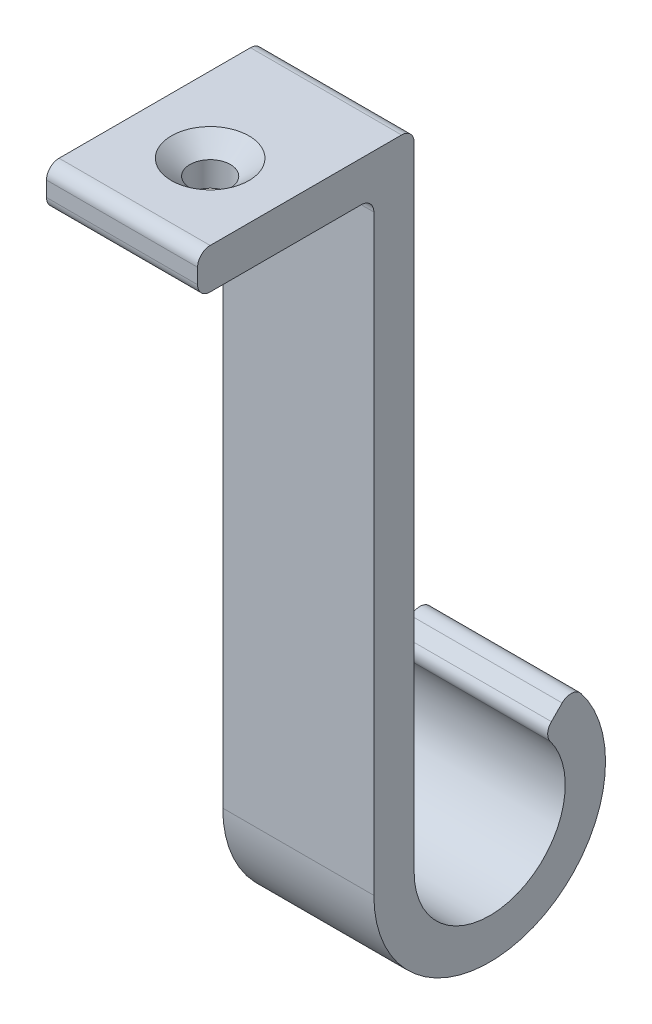
SolidWorks part; units mm, degrees
ref_plane "Front Plane" through (0, 0, 0) normal (0, 0, 1) x (1, 0, 0)
ref_plane "Top Plane" through (0, 0, 0) normal (0, 1, 0) x (1, 0, 0)
ref_plane "Right Plane" through (0, 0, 0) normal (1, 0, 0) x (0, 0, -1)
sketch "Sketch1" plane through (0, 0, 0) normal (1, 0, 0) x (0, 0, -1)
  line L0 (0, 0) -> (13.6525, -2.54) construction
  line L1 (-13.6525, -2.54) -> (8.5725, -2.54)
  line L2 (-13.6525, -2.54) -> (-13.6525, 2.54)
  line L3 (-13.6525, 2.54) -> (13.6525, 2.54)
  line L4 (13.6525, -78.74) -> (13.6525, 2.54)
  line L5 (-13.6525, -2.54) -> (13.6525, 2.54) construction
  line L6 (-13.6525, 2.54) -> (0, 0) construction
  line L7 (8.5725, -78.74) -> (13.6525, -78.74) construction
  line L8 (8.5725, -78.74) -> (8.5725, -2.54)
  line L9 (8.5725, -2.54) -> (13.6525, -2.54) construction
  line L11 (8.5725, -78.74) -> (13.6525, -2.54) construction
  line L12 (8.5725, -2.54) -> (13.6525, -78.74) construction
  line L13 (8.5725, -2.54) -> (13.6525, -2.54) construction
  line L14 (29.9127, -72.0048) -> (33.5048, -68.4127)
  arc A0 (8.5725, -78.74) -> (33.5048, -68.4127) centre (23.1775, -78.74) ccw
  arc A1 (13.6525, -78.74) -> (29.9127, -72.0048) centre (23.1775, -78.74) ccw
  point P0 (0, 0)
  point P6 (11.1125, -40.64)
  dimension "D4" = 9.525
  dimension "D1" = 5.08
  dimension "D2" = 22.225
  dimension "D3" = 76.2
  dimension "D5" = 45
extrude "Boss-Extrude1" add sketch "Sketch1" along normal mid plane 19.05
fillet "Fillet1" radius 1.5875 6 edges at (0, 2.54, 13.6525) (0, -2.54, 13.6525) (0, -2.54, -8.5725) (0, 2.54, -13.6525) (0, -68.4127, -33.5048) (0, -72.0048, -29.9127)
sketch "Sketch2" plane through (0, 2.54, 0) normal (0, 1, 0) x (1, 0, 0)
  line L0 (-9.525, 6.985) -> (9.525, -12.065) construction
  point P4 (0, -2.54)
hole_wizard "CSK for #10 Flat Head Machine Screw (100)1" positions "3DSketch1" profile "Sketch3" countersink size "#10" standard "ANSI Inch" end condition through all
sketch3d "3DSketch1"
  point P0 (0, 2.54, 2.54)
sketch "Sketch3" plane through (0, 2.54, 2.54) normal (1, 0, 0) x (0, 0, 1)
  line L0 (0, 0) -> (0, 95.885)
  line L1 (0, 95.885) -> (2.5527, 95.885)
  line L2 (2.5527, 95.885) -> (2.5527, 1.9608)
  line L3 (2.5527, 1.9608) -> (4.8895, 0)
  line L5 (4.8895, 0) -> (0, 0)
  line L6 (-2.5527, 1.9608) -> (-4.8895, 0) construction
  line L11 (0, -6.35) -> (0, 107.95) construction
  dimension "Thru Hole Dia." = 5.1054
  dimension "Thru Hole Depth" = 95.885
  dimension "Near C'Sink Dia." = 9.779
  dimension "Near C'Sink Angle" = 100
